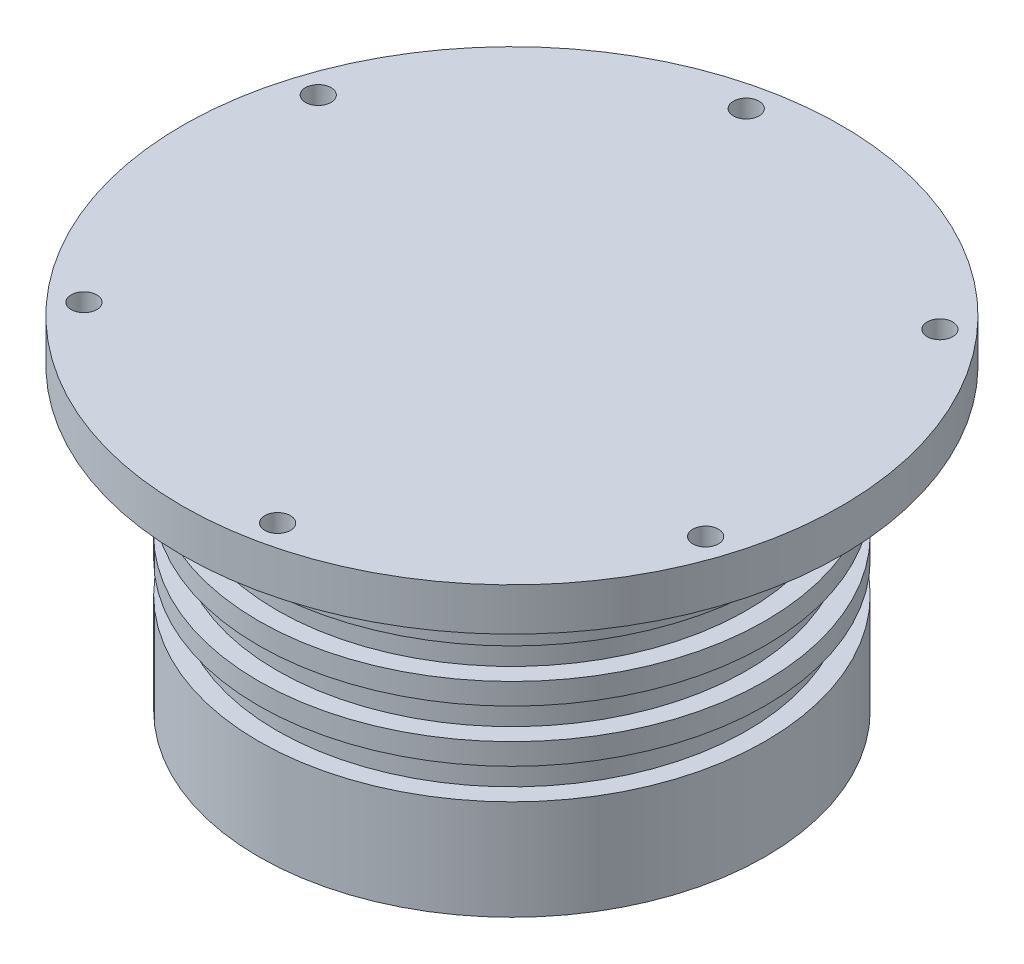
SolidWorks part; units mm, degrees
ref_plane "Plan de face" through (0, 0, 0) normal (0, 0, 1) x (1, 0, 0)
ref_plane "Plan de dessus" through (0, 0, 0) normal (0, 1, 0) x (1, 0, 0)
ref_plane "Plan de droite" through (0, 0, 0) normal (1, 0, 0) x (0, 0, -1)
sketch "Esquisse1" plane through (0, 0, 0) normal (0, 0, 1) x (1, 0, 0)
  line L0 (0, -164.0605) -> (0, 188.9811) construction
  line L1 (0, 93.9493) -> (77.14, 93.9493)
  line L2 (77.14, 93.9493) -> (77.14, 83.9493)
  line L3 (77.14, 83.9493) -> (59.3, 83.9493)
  line L4 (0, 93.9493) -> (0, 13.9493)
  line L5 (55, 83.9493) -> (55, -5.2068) construction
  line L6 (59.3, 49.5493) -> (59.3, 83.9493) construction
  line L7 (59.3, 83.9493) -> (59.3, 73.9493)
  line L8 (55, 68.9493) -> (55, 61.7493)
  line L9 (59.3, 73.9493) -> (59.3, 68.9493)
  line L10 (59.3, 68.9493) -> (55, 68.9493)
  line L11 (55, 61.7493) -> (59.3, 61.7493)
  line L12 (59.3, 61.7493) -> (59.3, 56.7493)
  line L13 (59.3, 56.7493) -> (55, 56.7493)
  line L14 (55, 56.7493) -> (55, 49.5493)
  line L15 (59.3, 49.5493) -> (59.3, 44.5493)
  line L16 (55, 49.5493) -> (59.3, 49.5493)
  line L17 (59.3, 44.5493) -> (55, 44.5493)
  line L18 (55, 13.9493) -> (0, 13.9493)
  line L19 (55, 44.5493) -> (55, 37.3493)
  line L20 (55, 13.9493) -> (59.3, 13.9493)
  line L21 (59.3, 13.9493) -> (59.3, 37.3493)
  line L22 (55, 37.3493) -> (59.3, 37.3493)
  dimension "D1" = 77.14
  dimension "D2" = 10
  dimension "D3" = 10
  dimension "D4" = 7.2
  dimension "D5" = 59.3
  dimension "D6" = 5
  dimension "D7" = 4.3
  dimension "D8" = 5
  dimension "D9" = 7.2
  dimension "D10" = 5
  dimension "D11" = 80
  dimension "D12" = 4.3
  dimension "D13" = 7.2
revolve "Révolution2" add sketch "Esquisse1" angle 360 about L4
sketch "Esquisse2" plane through (0, 0, 0) normal (0, 1, 0) x (1, 0, 0)
  line L1 (-52.8306, -47.3436) -> (14.5855, -69.4244)
  line L2 (14.5855, -69.4244) -> (67.416, -22.0808)
  line L3 (67.416, -22.0808) -> (52.8306, 47.3436)
  line L4 (52.8306, 47.3436) -> (-14.5855, 69.4244)
  line L5 (-14.5855, 69.4244) -> (-67.416, 22.0808)
  line L6 (-67.416, 22.0808) -> (-52.8306, -47.3436)
  circle A0 centre (0, 0) radius 70.94
  circle A1 centre (0, 0) radius 77.14 construction
  circle A2 centre (0, 0) radius 61.4358 construction
  circle A3 centre (14.5855, -69.4244) radius 3
  circle A4 centre (67.416, -22.0808) radius 3
  circle A5 centre (52.8306, 47.3436) radius 3
  circle A6 centre (-14.5855, 69.4244) radius 3
  circle A7 centre (-67.416, 22.0808) radius 3
  circle A8 centre (-52.8306, -47.3436) radius 3
  dimension "D1" = 6.2
  dimension "D2" = 6
  dimension "D3" = 70.94
  dimension "D4" = 6
  dimension "D5" = 6
  dimension "D6" = 6
  dimension "D7" = 6
  dimension "D8" = 6
  dimension "D9" = 70.94
  dimension "D10" = 70.94
extrude "Enlèv. mat.-Extru.1" cut sketch "Esquisse2" along normal blind 164 contours A8 | A3 | A4 | A5 | A6 | A7
